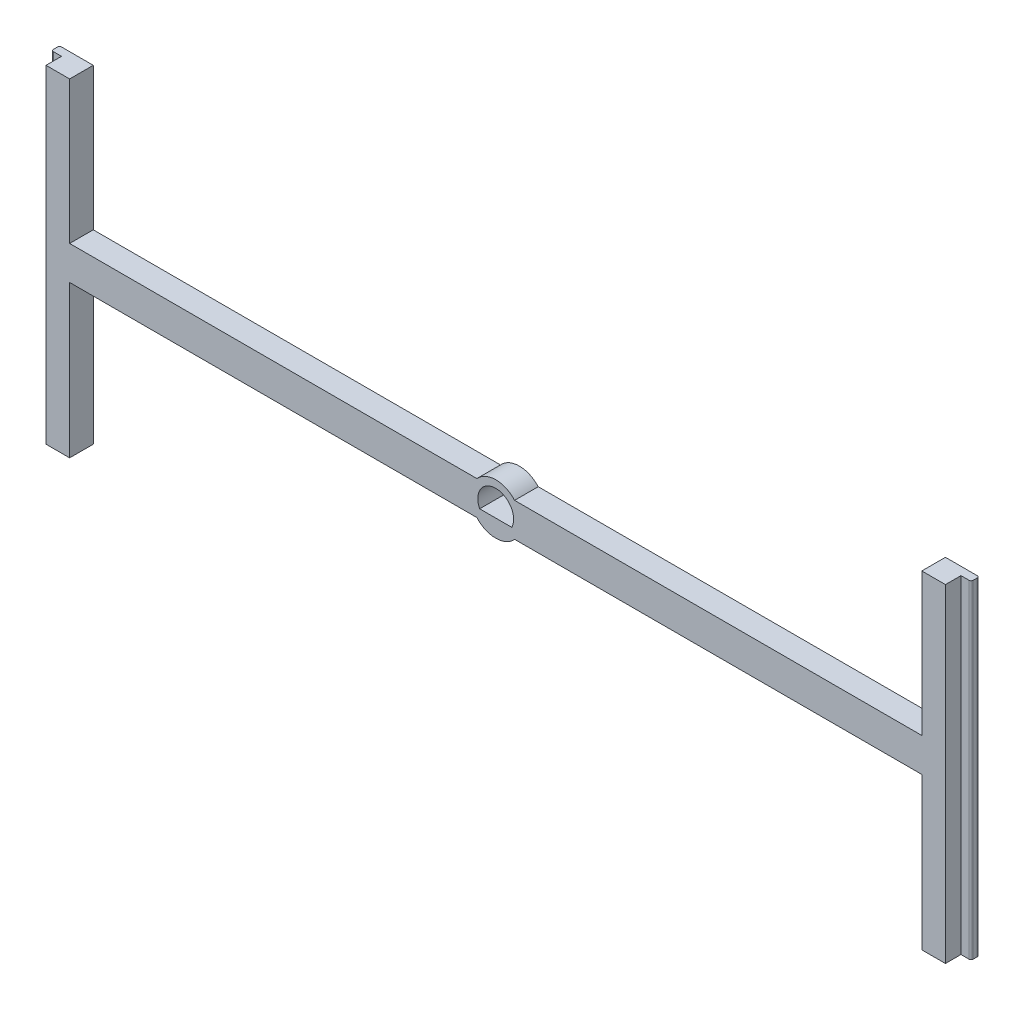
SolidWorks part; units mm, degrees
ref_plane "Front Plane" through (0, 0, 0) normal (0, 0, 1) x (1, 0, 0)
ref_plane "Top Plane" through (0, 0, 0) normal (0, 1, 0) x (1, 0, 0)
ref_plane "Right Plane" through (0, 0, 0) normal (1, 0, 0) x (0, 0, -1)
sketch "Sketch1" plane through (0, 0, 0) normal (0, 0, 1) x (1, 0, 0)
  line L0 (0, 2.5654) -> (0, -2.5654) construction
  line L1 (-63.1, 2.5) -> (-2.7951, 2.5)
  line L3 (-63.1, -2.5) -> (-2.7951, -2.5)
  line L5 (63.1, 25) -> (68.1, 25)
  line L6 (63.1, 25) -> (63.1, 2.5)
  line L7 (63.1, -25) -> (68.1, -25)
  line L8 (68.1, 25) -> (68.1, -25)
  line L9 (-63.1, -25) -> (-68.1, -25)
  line L10 (-68.1, 25) -> (-68.1, -25)
  line L11 (-63.1, 25) -> (-68.1, 25)
  line L12 (-63.1, 25) -> (-63.1, 2.5)
  line L13 (-63.1, -2.5) -> (-63.1, -25)
  line L14 (63.1, -2.5) -> (63.1, -25)
  line L15 (63.1, 2.5) -> (63.1, -2.5) construction
  line L17 (2.7951, 2.5) -> (63.1, 2.5)
  line L18 (2.7951, -2.5) -> (63.1, -2.5)
  line L19 (-2.3777, -1.17) -> (2.3777, -1.17)
  arc A1 (-2.7951, -2.5) -> (2.7951, -2.5) centre (0, 0) ccw
  arc A2 (2.3777, -1.17) -> (-2.3777, -1.17) centre (0, 0) ccw
  arc A3 (2.7951, 2.5) -> (-2.7951, 2.5) centre (0, 0) ccw
  point P20 (0, 2.65)
  point P23 (63.1, 0)
  point P24 (0, 0)
  point P25 (-68.1, 0)
  dimension "D5" = 3.82
  dimension "D7" = 7.5
  dimension "D6" = 2.65
  dimension "D1" = 126.2
  dimension "D2" = 5
  dimension "D3" = 50
  dimension "D4" = 5
extrude "Boss-Extrude1" add sketch "Sketch1" along normal blind 3.5
sketch "Sketch2" plane through (0, -25, 0) normal (0, -1, 0) x (1, 0, 0)
  line L0 (63.1, 3.5) -> (68.1, 3.5) construction
  line L5 (66.6, 3.5) -> (68.1, 3.5)
  line L6 (66.6, 3.5) -> (66.6, 1.2)
  line L7 (66.6, 1.2) -> (68.1, 1.2)
  line L8 (68.1, 3.5) -> (68.1, 1.2)
  line L9 (68.1, 3.5) -> (68.1, 0) construction
  line L10 (0, 0) -> (0, -12.1014) construction
  line L11 (-2.7951, 0) -> (2.7951, 0) construction
  line L12 (-66.6, 1.2) -> (-68.1, 1.2)
  line L13 (-68.1, 3.5) -> (-68.1, 1.2)
  line L14 (-66.6, 3.5) -> (-66.6, 1.2)
  line L15 (-66.6, 3.5) -> (-68.1, 3.5)
  line L16 (63.1, 0) -> (68.1, 0) construction
  dimension "D1" = 1.5
  dimension "D2" = 1.2
extrude "Cut-Extrude1" cut sketch "Sketch2" against normal through all
sketch "Sketch3" plane through (0, 0, 3.5) normal (0, 0, 1) x (1, 0, 0)
  line L0 (68.1, 25) -> (68.1, -25) construction
  line L1 (-68.1, 25) -> (68.1, 25)
  line L2 (-68.1, 25) -> (-68.1, 23.6)
  line L3 (-68.1, 23.6) -> (68.1, 23.6)
  line L4 (68.1, 25) -> (68.1, 23.6)
  dimension "D1" = 1.4
extrude "Cut-Extrude2" cut sketch "Sketch3" against normal through all
fillet "Fillet1" radius 0.3 4 edges at (68.1, -0.7, 0) (68.1, -0.7, 1.2) (-68.1, -0.7, 0) (-68.1, -0.7, 1.2)
